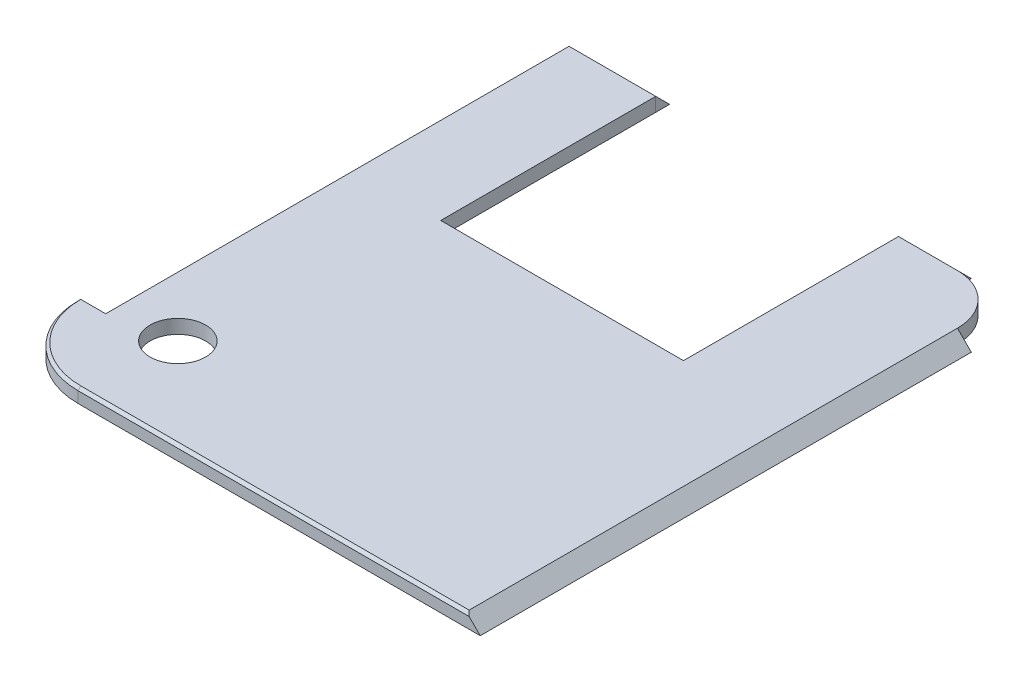
SolidWorks part; units mm, degrees
ref_plane "前视基准面" through (0, 0, 0) normal (0, 0, 1) x (1, 0, 0)
ref_plane "上视基准面" through (0, 0, 0) normal (0, 1, 0) x (1, 0, 0)
ref_plane "右视基准面" through (0, 0, 0) normal (1, 0, 0) x (0, 0, -1)
other "Configuration Table"
sketch "草图1" plane through (0, 0, 0) normal (0, 1, 0) x (1, 0, 0)
  line L0 (-14.1799, -20.3117) -> (-14.1799, -14.7117) construction
  line L5 (-14.1799, -14.7117) -> (-10.5799, -14.7117) construction
  line L6 (17.4201, 18.6883) -> (13.8201, 18.6883) construction
  line L7 (13.8201, 18.6883) -> (13.8201, 15.0883) construction
  line L8 (-14.1799, 18.6883) -> (13.8201, 18.6883)
  line L9 (17.4201, 15.0883) -> (17.4201, -20.3117)
  line L10 (-14.1799, 18.6883) -> (-14.1799, -14.7117)
  line L11 (-14.1799, -14.7117) -> (-16.1799, -14.7117)
  line L12 (-10.5799, -20.3117) -> (17.4201, -20.3117)
  arc A0 (-16.1799, -14.7117) -> (-10.5799, -20.3117) centre (-10.5799, -14.7117) ccw
  arc A1 (17.4201, 15.0883) -> (13.8201, 18.6883) centre (13.8201, 15.0883) ccw
  dimension "D1" = 39
  dimension "D2" = 31.6
extrude "凸台-拉伸1" add sketch "草图1" along normal blind 1
sketch "草图2" plane through (0, 0, 14.7117) normal (0, 0, -1) x (-1, 0, 0)
  line L0 (14.1799, 1) -> (14.1799, 0)
  line L1 (14.1799, 0) -> (15.1799, 0)
  line L2 (14.1799, 0) -> (16.1799, 0) construction
  line L3 (15.1799, 0) -> (14.1799, 1)
extrude "凸台-拉伸2" add sketch "草图2" along normal blind 33.4 separate body
sketch "草图3" plane through (-14.1799, 0, 0) normal (-1, 0, 0) x (0, 0, 1)
  line L0 (-18.6883, 1) -> (-18.6883, 0)
  line L1 (-18.6883, 0) -> (-19.6883, 0)
  line L2 (-19.6883, 0) -> (-18.6883, 1)
extrude "凸台-拉伸3" add sketch "草图3" against normal blind 6.25 separate body
ref_plane "基准面1" through (13.8201, 0, 0) normal (-1, 0, 0) x (0, 0, 1)
sketch "草图4" plane through (13.8201, 0, 0) normal (-1, 0, 0) x (0, 0, 1)
  line L0 (-18.6883, 1) -> (-18.6883, 0)
  line L1 (-18.6883, 0) -> (-19.6883, 0)
  line L2 (-19.6883, 0) -> (-18.6883, 1)
extrude "凸台-拉伸4" add sketch "草图4" along normal blind 4.25 separate body
sketch "草图5" plane through (0, 0, 20.3117) normal (0, 0, 1) x (1, 0, 0)
  line L0 (17.4201, 1) -> (17.4201, 0)
  line L1 (17.4201, 0) -> (18.4201, 0)
  line L2 (18.4201, 0) -> (17.4201, 1)
extrude "凸台-拉伸5" add sketch "草图5" against normal blind 35.4
sketch "草图6" plane through (0, 1, 0) normal (0, 1, 0) x (1, 0, 0)
  line L1 (-7.9299, 18.6883) -> (9.5701, 18.6883)
  line L2 (-7.9299, 18.6883) -> (-7.9299, 3.1883)
  line L3 (-7.9299, 3.1883) -> (9.5701, 3.1883)
  line L4 (9.5701, 18.6883) -> (9.5701, 3.1883)
  dimension "D1" = 15.5
  dimension "D2" = 17.5
extrude "切除-拉伸1" cut sketch "草图6" against normal through all
sketch "草图7" plane through (0, 0, 0) normal (0, -1, 0) x (1, 0, 0)
  line L0 (-16.1799, 14.7117) -> (-1.1799, 14.7117) construction
  line L1 (-10.5799, 20.3117) -> (18.4201, 20.3117) construction
  line L3 (-1.1799, 20.3117) -> (-1.1799, 10.3117) construction
  line L5 (-1.1799, 10.3117) -> (4.4201, 10.3117)
  line L6 (-1.1799, 10.3117) -> (-1.1799, 4.7117)
  line L7 (-1.1799, 4.7117) -> (4.4201, 4.7117)
  line L8 (4.4201, 10.3117) -> (4.4201, 4.7117)
  dimension "D1" = 5.6
  dimension "D2" = 5.6
extrude "凸台-拉伸6" add sketch "草图7" along normal blind 5
sketch "草图8" plane through (0, -5, 0) normal (0, -1, 0) x (1, 0, 0)
  circle A0 centre (1.6201, 7.5117) radius 1
chamfer "倒角2" distance 1 angle 45 4 edges at (1.6201, -5, 4.7117) (4.4201, -5, 7.5117) (1.6201, -5, 10.3117) (-1.1799, -5, 7.5117)
chamfer "倒角3" distance 0.2 angle 45 2 edges at (3.4201, 1, 20.3117) (-14.5397, 1, 18.6715)
sketch "草图9" plane through (0, 1, 0) normal (0, 1, 0) x (1, 0, 0)
  line L0 (-16.1799, -14.7117) -> (-9.8799, -14.7117) construction
  line L1 (-10.5799, -20.1117) -> (-10.5799, -13.8117) construction
  circle A1 centre (-9.8799, -13.8117) radius 2
  dimension "D1" = 6.3
  dimension "D2" = 6.3
extrude "切除-拉伸3" cut sketch "草图9" against normal up to next (1 mm away)
